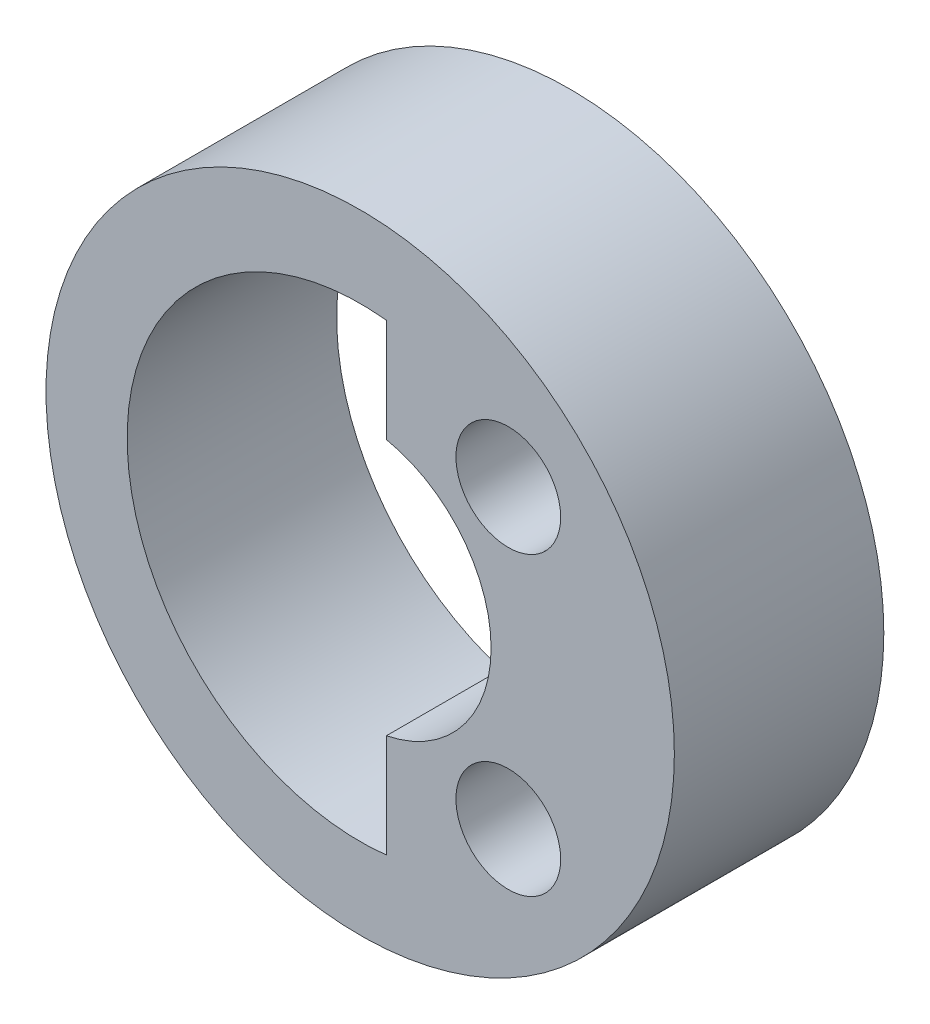
SolidWorks part; units mm, degrees
material "ABS"
ref_plane "Front Plane" through (0, 0, 0) normal (0, 0, 1) x (1, 0, 0)
ref_plane "Top Plane" through (0, 0, 0) normal (0, 1, 0) x (1, 0, 0)
ref_plane "Right Plane" through (0, 0, 0) normal (1, 0, 0) x (0, 0, -1)
sketch "Sketch1" plane through (0, 0, 0) normal (0, 0, 1) x (1, 0, 0)
  circle A0 centre (0, 0) radius 3
  dimension "D1" = 6
extrude "Boss-Extrude1" add sketch "Sketch1" along normal blind 2 from surface contours A0
sketch "Sketch2" plane through (0, 0, -0.1) normal (0, 0, 1) x (1, 0, 0)
  line L0 (0.25, 1.2247) -> (0.25, 2.2109)
  line L1 (0.25, -2.2109) -> (0.25, -1.2247)
  line L2 (0, 1) -> (0, 1.975)
  line L3 (0, -1.975) -> (0, -1)
  line L4 (0, 1) -> (0, 1.975) construction
  line L5 (0, -1.975) -> (0, -1) construction
  arc A0 (0.25, 2.2109) -> (0.25, -2.2109) centre (0, 0) ccw
  arc A1 (0.25, -1.2247) -> (0.25, 1.2247) centre (0, 0) ccw
  arc A2 (0, 1.975) -> (0, -1.975) centre (0, 0) ccw
  arc A3 (0, -1) -> (0, 1) centre (0, 0) ccw
  arc A4 (0, 1.975) -> (0, -1.975) centre (0, 0) ccw construction
  arc A5 (0, -1) -> (0, 1) centre (0, 0) ccw construction
  dimension "D1" = 0
  dimension "D2" = 0.25
extrude "Cut-Extrude1" cut sketch "Sketch2" against normal through all contours A1 L0 A0 L1
sketch "Sketch3" plane through (0, 0, -0.1) normal (0, 0, 1) x (1, 0, 0)
  line L0 (0, 0) -> (1.4142, 1.4142) construction
  line L1 (0, 0) -> (0, 3) construction
  circle A0 centre (1.4142, 1.4142) radius 0.5
  circle A1 centre (0, 0) radius 3 construction
  dimension "D1" = 1
  dimension "D2" = 2
  dimension "D3" = 45
extrude "Cut-Extrude2" cut sketch "Sketch3" against normal through all
mirror "Mirror1" about plane through (0, 0, 0) normal (0, 1, 0) of "Cut-Extrude2"
sketch "Sketch5" plane through (0, 0, -0.1) normal (0, 0, 1) x (1, 0, 0)
  line L0 (0.17, -2.1383) -> (0.17, -1.1576)
  line L1 (0.17, 1.1576) -> (0.17, 2.1383)
  line L2 (0.25, -2.2109) -> (0.25, -1.2247)
  line L3 (0.25, 1.2247) -> (0.25, 2.2109)
  line L4 (0.25, -2.2109) -> (0.25, -1.2247)
  line L5 (0.25, 1.2247) -> (0.25, 2.2109)
  arc A0 (0.17, -1.1576) -> (0.17, 1.1576) centre (0, 0) ccw
  arc A1 (0.17, 2.1383) -> (0.17, -2.1383) centre (0, 0) ccw
  arc A2 (0.25, 2.2109) -> (0.25, -2.2109) centre (0, 0) ccw
  arc A3 (0.25, -1.2247) -> (0.25, 1.2247) centre (0, 0) ccw
  arc A4 (0.25, 2.2109) -> (0.25, -2.2109) centre (0, 0) ccw
  arc A5 (0.25, -1.2247) -> (0.25, 1.2247) centre (0, 0) ccw
  dimension "D1" = 0
  dimension "D2" = 0.08
extrude "Boss-Extrude2" [suppressed] add sketch "Sketch5" against normal up to surface (2 mm away)
